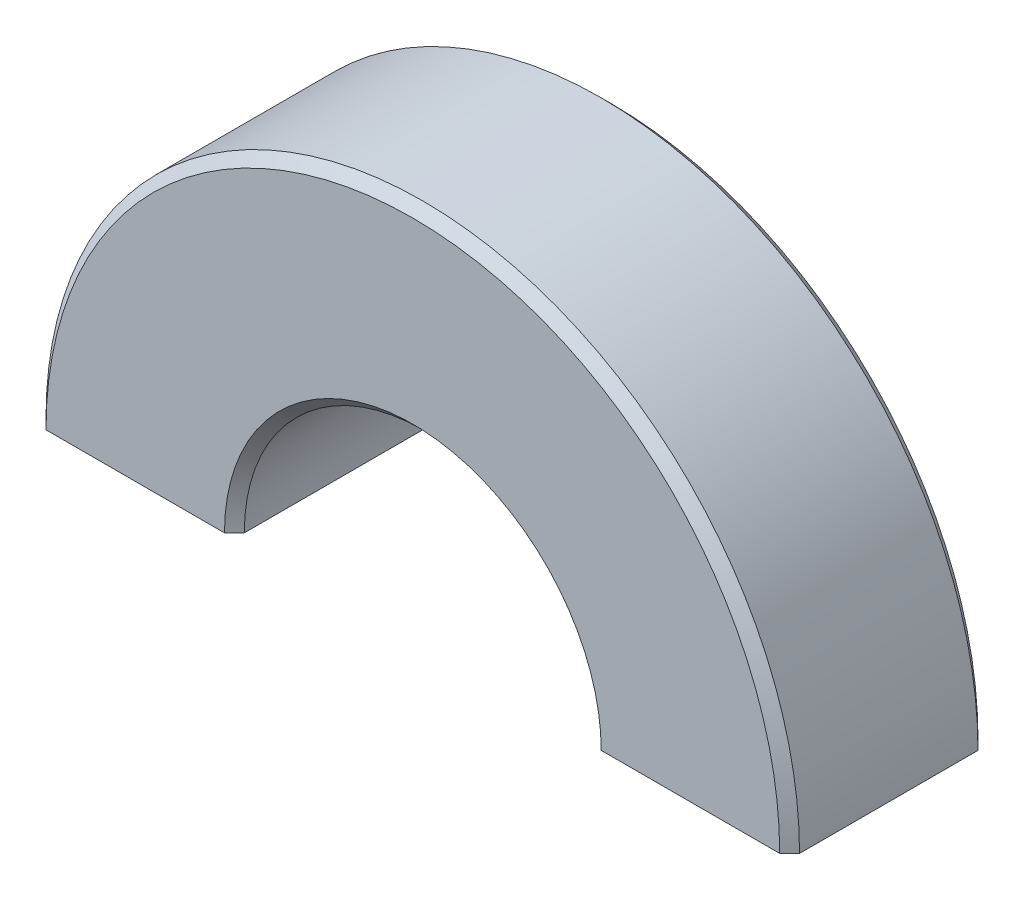
SolidWorks part; units mm, degrees
ref_plane "Front Plane" through (0, 0, 0) normal (0, 0, 1) x (1, 0, 0)
ref_plane "Top Plane" through (0, 0, 0) normal (0, 1, 0) x (1, 0, 0)
ref_plane "Right Plane" through (0, 0, 0) normal (1, 0, 0) x (0, 0, -1)
sketch "Sketch1" plane through (0, 0, 0) normal (0, 0, 1) x (1, 0, 0)
  line L0 (-9, 0) -> (-19, 0)
  line L1 (9, 0) -> (19, 0)
  arc A0 (19, 0) -> (-19, 0) centre (0, 0) ccw
  arc A1 (9, 0) -> (-9, 0) centre (0, 0) ccw
  dimension "D1" = 9
  dimension "D2" = 19
extrude "Boss-Extrude1" add sketch "Sketch1" along normal blind 10
chamfer "Chamfer1" distance 0.5 4 edges at (0, 19, 0) (0, 9, 0) (0, 9, 10) (0, 19, 10)
